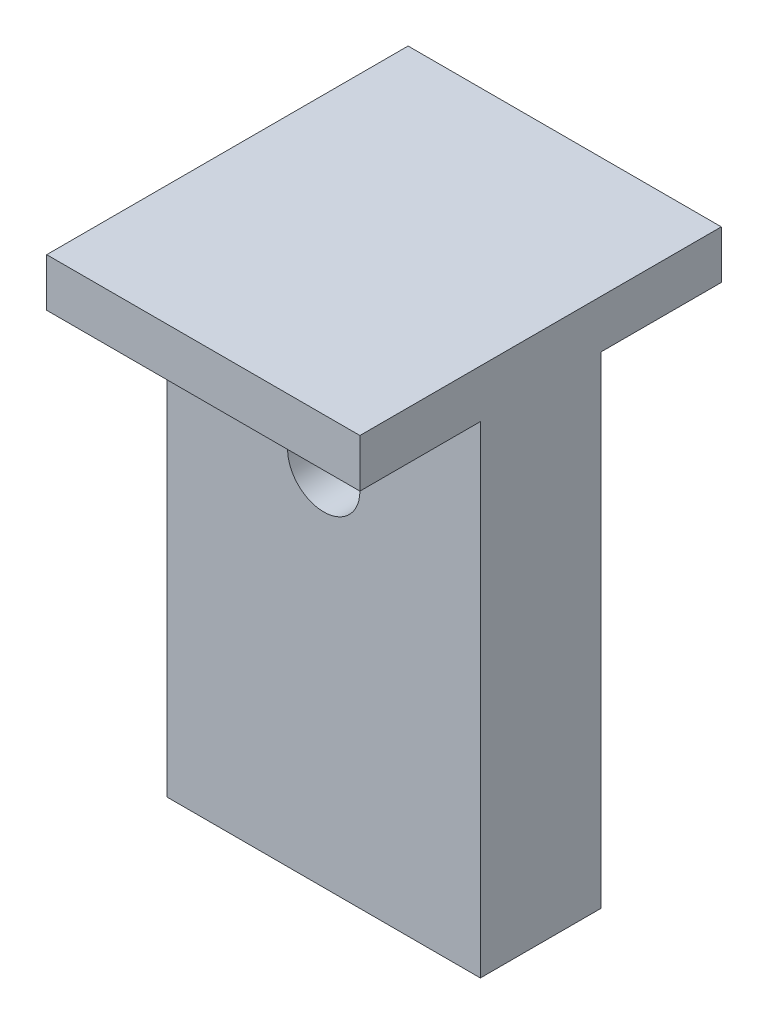
SolidWorks part; units mm, degrees
ref_plane "Front Plane" through (0, 0, 0) normal (0, 0, 1) x (1, 0, 0)
ref_plane "Top Plane" through (0, 0, 0) normal (0, 1, 0) x (1, 0, 0)
ref_plane "Right Plane" through (0, 0, 0) normal (1, 0, 0) x (0, 0, -1)
sketch "Sketch1" plane through (0, 0, 0) normal (0, 1, 0) x (1, 0, 0)
  line L1 (-6.5, 2.5) -> (6.5, 2.5)
  line L2 (-6.5, 2.5) -> (-6.5, -2.5)
  line L3 (-6.5, -2.5) -> (6.5, -2.5)
  line L4 (6.5, 2.5) -> (6.5, -2.5)
  line L5 (-6.5, 2.5) -> (6.5, -2.5) construction
  line L6 (-6.5, -2.5) -> (6.5, 2.5) construction
  point P0 (0, 0)
  dimension "D1" = 5
  dimension "D2" = 13
extrude "Boss-Extrude1" add sketch "Sketch1" along normal blind 20
hole_wizard "M2 Tapped Hole1" positions "3DSketch1" profile "Sketch3" tap size "M2" standard "ISO"
sketch3d "3DSketch1"
  point P0 (0, 0, 0)
  point P3 (0, 0, 0)
sketch "Sketch3" plane through (0, 0, 0) normal (1, 0, 0) x (0, 0, -1)
  line L0 (0, 0) -> (0, 5.6807)
  line L1 (0, 5.6807) -> (0.8, 5.2)
  line L2 (0.8, 5.2) -> (0.8, 0)
  line L5 (0.8, 0) -> (0, 0)
  line L10 (0, 5.6807) -> (-0.8, 5.2) construction
  line L11 (0, -6.35) -> (0, 107.95) construction
  dimension "Tap Drill Dia." = 1.6
  dimension "Tap Drill Depth" = 5.2
  dimension "Drill Angle" = 118
cosmetic thread "Hole Thread1" parameters "D1"=4, "D2"=2
hole_wizard "Ø1.0mm Dowel Hole1" positions "3DSketch2" profile "Sketch4" hole size "Ø1.0" standard "ISO"
sketch3d "3DSketch2"
  point P0 (-5, 0, 0)
  dimension "D1" = 5
sketch "Sketch4" plane through (-5, 0, 0) normal (1, 0, 0) x (0, 0, -1)
  line L0 (0, 0) -> (0, 4.3004)
  line L1 (0, 4.3004) -> (0.5, 4)
  line L2 (0.5, 4) -> (0.5, 0)
  line L5 (0.5, 0) -> (0, 0)
  line L10 (0, 4.3004) -> (-0.5, 4) construction
  line L11 (0, -6.35) -> (0, 107.95) construction
  dimension "Hole Dia." = 1
  dimension "Hole Depth" = 4
  dimension "Drill Angle" = 118
mirror "Mirror1" about plane through (0, 0, 0) normal (1, 0, 0) of "Ø1.0mm Dowel Hole1"
hole_wizard "Ø3.0 (3) Diameter Hole1" positions "3DSketch3" profile "Sketch5" hole size "Ø3.0" standard "ISO" end condition through all
sketch3d "3DSketch3"
  line L0 (-6.5, 20, 2.5) -> (6.5, 20, 2.5) construction
  point P0 (0, 15, 2.5)
  point P3 (0, 0, 0)
  dimension "D1" = 5
sketch "Sketch5" plane through (0, 15, 2.5) normal (1, 0, 0) x (0, -1, 0)
  line L0 (0, 0) -> (0, 5)
  line L1 (0, 5) -> (1.5, 5)
  line L2 (1.5, 5) -> (1.5, 0)
  line L5 (1.5, 0) -> (0, 0)
  line L11 (0, -6.35) -> (0, 107.95) construction
  dimension "Thru Hole Dia." = 3
  dimension "Thru Hole Depth" = 5
sketch "Sketch7" plane through (0, 20, 0) normal (0, 1, 0) x (1, 0, 0)
  line L0 (-6.5, 2.5) -> (-6.5, -2.5) construction
  line L1 (6.5, 7.5) -> (-6.5, 7.5)
  line L2 (6.5, 7.5) -> (6.5, -7.5)
  line L3 (6.5, -7.5) -> (-6.5, -7.5)
  line L4 (-6.5, 7.5) -> (-6.5, -7.5)
  line L5 (6.5, 7.5) -> (-6.5, -7.5) construction
  line L6 (6.5, -7.5) -> (-6.5, 7.5) construction
  point P0 (0, 0)
  dimension "D1" = 15
extrude "Boss-Extrude2" add sketch "Sketch7" along normal blind 2
